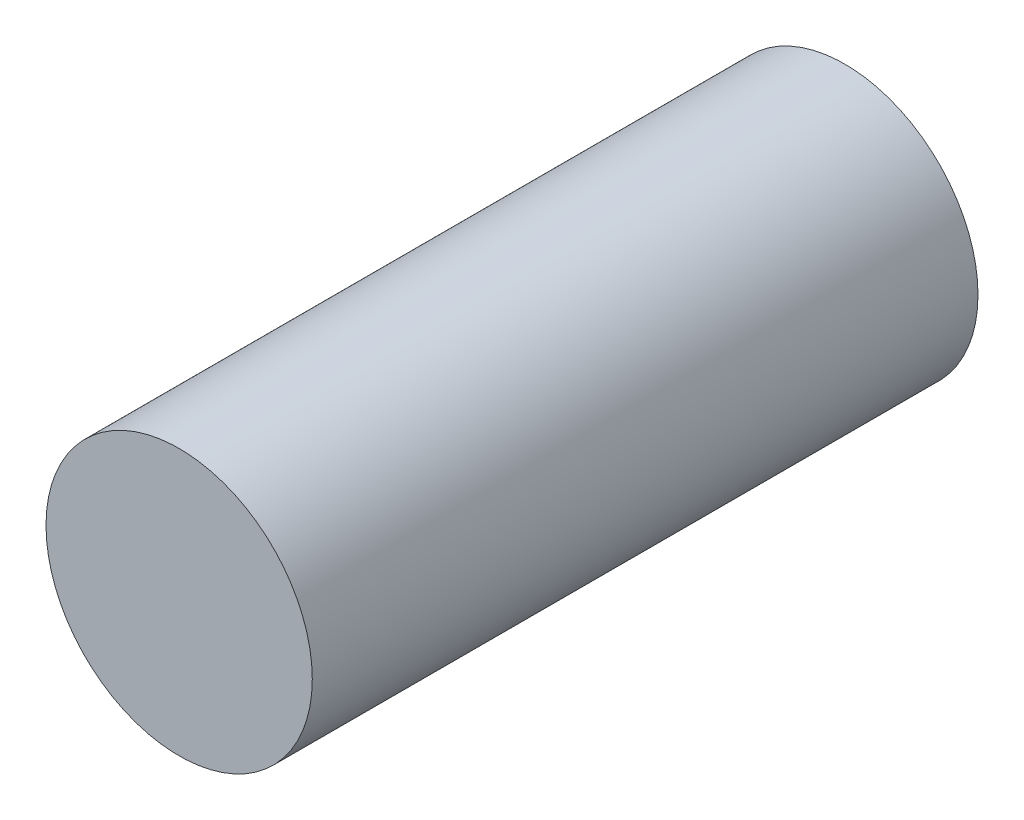
SolidWorks part; units mm, degrees
ref_plane "Front Plane" through (0, 0, 0) normal (0, 0, 1) x (1, 0, 0)
ref_plane "Top Plane" through (0, 0, 0) normal (0, 1, 0) x (1, 0, 0)
ref_plane "Right Plane" through (0, 0, 0) normal (1, 0, 0) x (0, 0, -1)
sketch "Sketch1" plane through (0, 0, 0) normal (0, 0, 1) x (1, 0, 0)
  circle A0 centre (0, 0) radius 25.4
  dimension "D1" = 50.8
extrude "Boss-Extrude1" add sketch "Sketch1" against normal blind 127
